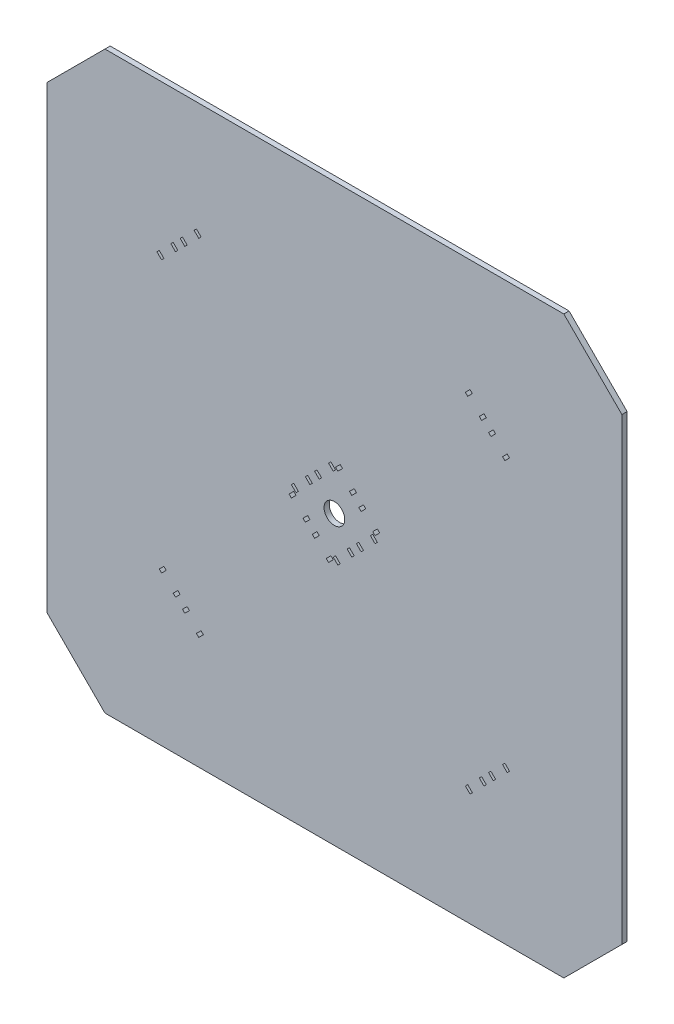
SolidWorks part; units mm, degrees
ref_plane "Front Plane" through (0, 0, 0) normal (0, 0, 1) x (1, 0, 0)
ref_plane "Top Plane" through (0, 0, 0) normal (0, 1, 0) x (1, 0, 0)
ref_plane "Right Plane" through (0, 0, 0) normal (1, 0, 0) x (0, 0, -1)
sketch "Model" plane through (0, 0, 0) normal (0, 0, 1) x (1, 0, 0)
  line L0 (0, 17.6777) -> (0, 157.3223)
  line L1 (17.6777, 175) -> (157.3223, 175)
  line L2 (175, 157.3223) -> (175, 17.6777)
  line L3 (157.3223, 0) -> (17.6777, 0)
  line L4 (139.3817, 47.6391) -> (140.7959, 46.2249)
  line L5 (140.7959, 46.2249) -> (140.0888, 45.5178)
  line L6 (140.0888, 45.5178) -> (138.6746, 46.932)
  line L7 (138.6746, 46.932) -> (139.3817, 47.6391)
  line L8 (135.1391, 43.3964) -> (136.5533, 41.9822)
  line L9 (136.5533, 41.9822) -> (135.8462, 41.2751)
  line L10 (135.8462, 41.2751) -> (134.432, 42.6893)
  line L11 (134.432, 42.6893) -> (135.1391, 43.3964)
  line L12 (132.3107, 40.568) -> (133.7249, 39.1538)
  line L13 (133.7249, 39.1538) -> (133.0178, 38.4467)
  line L14 (133.0178, 38.4467) -> (131.6036, 39.8609)
  line L15 (131.6036, 39.8609) -> (132.3107, 40.568)
  line L16 (128.068, 36.3254) -> (129.4822, 34.9112)
  line L17 (129.4822, 34.9112) -> (128.7751, 34.2041)
  line L18 (128.7751, 34.2041) -> (127.3609, 35.6183)
  line L19 (127.3609, 35.6183) -> (128.068, 36.3254)
  line L20 (87.8536, 76.5398) -> (89.2678, 75.1256)
  line L21 (89.2678, 75.1256) -> (88.5607, 74.4185)
  line L22 (88.5607, 74.4185) -> (87.1464, 75.8327)
  line L23 (87.1464, 75.8327) -> (87.8536, 76.5398)
  line L24 (92.0962, 80.7825) -> (93.5104, 79.3683)
  line L25 (93.5104, 79.3683) -> (92.8033, 78.6612)
  line L26 (92.8033, 78.6612) -> (91.3891, 80.0754)
  line L27 (91.3891, 80.0754) -> (92.0962, 80.7825)
  line L28 (47.6391, 35.6183) -> (46.2249, 34.2041)
  line L29 (46.2249, 34.2041) -> (45.5178, 34.9112)
  line L30 (45.5178, 34.9112) -> (46.932, 36.3254)
  line L31 (46.932, 36.3254) -> (47.6391, 35.6183)
  line L32 (43.3964, 39.8609) -> (41.9822, 38.4467)
  line L33 (41.9822, 38.4467) -> (41.2751, 39.1538)
  line L34 (41.2751, 39.1538) -> (42.6893, 40.568)
  line L35 (42.6893, 40.568) -> (43.3964, 39.8609)
  line L36 (40.568, 42.6893) -> (39.1538, 41.2751)
  line L37 (39.1538, 41.2751) -> (38.4467, 41.9822)
  line L38 (38.4467, 41.9822) -> (39.8609, 43.3964)
  line L39 (39.8609, 43.3964) -> (40.568, 42.6893)
  line L40 (36.3254, 46.932) -> (34.9112, 45.5178)
  line L41 (34.9112, 45.5178) -> (34.2041, 46.2249)
  line L42 (34.2041, 46.2249) -> (35.6183, 47.6391)
  line L43 (35.6183, 47.6391) -> (36.3254, 46.932)
  line L44 (75.8327, 86.4393) -> (74.4185, 85.0251)
  line L45 (74.4185, 85.0251) -> (73.7114, 85.7322)
  line L46 (73.7114, 85.7322) -> (75.1256, 87.1464)
  line L47 (75.1256, 87.1464) -> (75.8327, 86.4393)
  line L48 (80.0754, 82.1967) -> (78.6612, 80.7825)
  line L49 (78.6612, 80.7825) -> (77.9541, 81.4896)
  line L50 (77.9541, 81.4896) -> (79.3683, 82.9038)
  line L51 (79.3683, 82.9038) -> (80.0754, 82.1967)
  line L52 (82.9038, 79.3683) -> (81.4896, 77.9541)
  line L53 (81.4896, 77.9541) -> (80.7825, 78.6612)
  line L54 (80.7825, 78.6612) -> (82.1967, 80.0754)
  line L55 (82.1967, 80.0754) -> (82.9038, 79.3683)
  line L56 (87.1464, 75.1256) -> (85.7322, 73.7114)
  line L57 (85.7322, 73.7114) -> (85.0251, 74.4185)
  line L58 (85.0251, 74.4185) -> (86.4393, 75.8327)
  line L59 (86.4393, 75.8327) -> (87.1464, 75.1256)
  line L60 (101.2886, 89.2678) -> (99.8744, 87.8536)
  line L61 (99.8744, 87.8536) -> (99.1673, 88.5607)
  line L62 (99.1673, 88.5607) -> (100.5815, 89.9749)
  line L63 (100.5815, 89.9749) -> (101.2886, 89.2678)
  line L64 (97.0459, 93.5104) -> (95.6317, 92.0962)
  line L65 (95.6317, 92.0962) -> (94.9246, 92.8033)
  line L66 (94.9246, 92.8033) -> (96.3388, 94.2175)
  line L67 (96.3388, 94.2175) -> (97.0459, 93.5104)
  line L68 (94.2175, 96.3388) -> (92.8033, 94.9246)
  line L69 (92.8033, 94.9246) -> (92.0962, 95.6317)
  line L70 (92.0962, 95.6317) -> (93.5104, 97.0459)
  line L71 (93.5104, 97.0459) -> (94.2175, 96.3388)
  line L72 (89.9749, 100.5815) -> (88.5607, 99.1673)
  line L73 (88.5607, 99.1673) -> (87.8536, 99.8744)
  line L74 (87.8536, 99.8744) -> (89.2678, 101.2886)
  line L75 (89.2678, 101.2886) -> (89.9749, 100.5815)
  line L76 (129.4822, 140.0888) -> (128.068, 138.6746)
  line L77 (128.068, 138.6746) -> (127.3609, 139.3817)
  line L78 (127.3609, 139.3817) -> (128.7751, 140.7959)
  line L79 (128.7751, 140.7959) -> (129.4822, 140.0888)
  line L80 (133.7249, 135.8462) -> (132.3107, 134.432)
  line L81 (132.3107, 134.432) -> (131.6036, 135.1391)
  line L82 (131.6036, 135.1391) -> (133.0178, 136.5533)
  line L83 (133.0178, 136.5533) -> (133.7249, 135.8462)
  line L84 (136.5533, 133.0178) -> (135.1391, 131.6036)
  line L85 (135.1391, 131.6036) -> (134.432, 132.3107)
  line L86 (134.432, 132.3107) -> (135.8462, 133.7249)
  line L87 (135.8462, 133.7249) -> (136.5533, 133.0178)
  line L88 (140.7959, 128.7751) -> (139.3817, 127.3609)
  line L89 (139.3817, 127.3609) -> (138.6746, 128.068)
  line L90 (138.6746, 128.068) -> (140.0888, 129.4822)
  line L91 (140.0888, 129.4822) -> (140.7959, 128.7751)
  line L92 (94.9246, 83.6109) -> (96.3388, 82.1967)
  line L93 (96.3388, 82.1967) -> (95.6317, 81.4896)
  line L94 (95.6317, 81.4896) -> (94.2175, 82.9038)
  line L95 (94.2175, 82.9038) -> (94.9246, 83.6109)
  line L96 (99.1673, 87.8536) -> (100.5815, 86.4393)
  line L97 (100.5815, 86.4393) -> (99.8744, 85.7322)
  line L98 (99.8744, 85.7322) -> (98.4602, 87.1464)
  line L99 (98.4602, 87.1464) -> (99.1673, 87.8536)
  line L100 (75.1256, 89.2678) -> (76.5398, 87.8536)
  line L101 (76.5398, 87.8536) -> (75.8327, 87.1464)
  line L102 (75.8327, 87.1464) -> (74.4185, 88.5607)
  line L103 (74.4185, 88.5607) -> (75.1256, 89.2678)
  line L104 (79.3683, 93.5104) -> (80.7825, 92.0962)
  line L105 (80.7825, 92.0962) -> (80.0754, 91.3891)
  line L106 (80.0754, 91.3891) -> (78.6612, 92.8033)
  line L107 (78.6612, 92.8033) -> (79.3683, 93.5104)
  line L108 (82.1967, 96.3388) -> (83.6109, 94.9246)
  line L109 (83.6109, 94.9246) -> (82.9038, 94.2175)
  line L110 (82.9038, 94.2175) -> (81.4896, 95.6317)
  line L111 (81.4896, 95.6317) -> (82.1967, 96.3388)
  line L112 (86.4393, 100.5815) -> (87.8536, 99.1673)
  line L113 (87.8536, 99.1673) -> (87.1464, 98.4602)
  line L114 (87.1464, 98.4602) -> (85.7322, 99.8744)
  line L115 (85.7322, 99.8744) -> (86.4393, 100.5815)
  line L116 (34.2041, 130.1893) -> (35.6183, 128.7751)
  line L117 (35.6183, 128.7751) -> (34.9112, 128.068)
  line L118 (34.9112, 128.068) -> (33.497, 129.4822)
  line L119 (33.497, 129.4822) -> (34.2041, 130.1893)
  line L120 (38.4467, 134.432) -> (39.8609, 133.0178)
  line L121 (39.8609, 133.0178) -> (39.1538, 132.3107)
  line L122 (39.1538, 132.3107) -> (37.7396, 133.7249)
  line L123 (37.7396, 133.7249) -> (38.4467, 134.432)
  line L124 (41.2751, 137.2604) -> (42.6893, 135.8462)
  line L125 (42.6893, 135.8462) -> (41.9822, 135.1391)
  line L126 (41.9822, 135.1391) -> (40.568, 136.5533)
  line L127 (40.568, 136.5533) -> (41.2751, 137.2604)
  line L128 (45.5178, 141.503) -> (46.932, 140.0888)
  line L129 (46.932, 140.0888) -> (46.2249, 139.3817)
  line L130 (46.2249, 139.3817) -> (44.8107, 140.7959)
  line L131 (44.8107, 140.7959) -> (45.5178, 141.503)
  line L132 (17.6777, 0) -> (0, 17.6777)
  line L133 (157.3223, 0) -> (175, 17.6777)
  line L134 (157.3223, 175) -> (175, 157.3223)
  line L135 (17.6777, 175) -> (0, 157.3223)
  circle A0 centre (87.5, 87.5) radius 3.15
  dimension "D1" = 135
  dimension "D2" = 135
  dimension "D3" = 135
  dimension "D4" = 25
  dimension "D5" = 25
  dimension "D6" = 25
  dimension "D7" = 25
extrude "Boss-Extrude1" add sketch "Model" along normal blind 1.59
